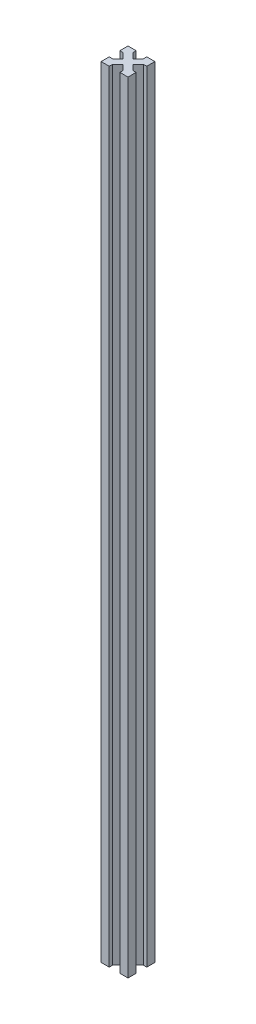
SolidWorks part; units mm, degrees
ref_plane "Plan de face" through (0, 0, 0) normal (0, 0, 1) x (1, 0, 0)
ref_plane "Plan de dessus" through (0, 0, 0) normal (0, 1, 0) x (1, 0, 0)
ref_plane "Plan de droite" through (0, 0, 0) normal (1, 0, 0) x (0, 0, -1)
sketch "Esquisse1" plane through (0, 0, 0) normal (0, 1, 0) x (1, 0, 0)
  line L0 (-2.5, 17.5) -> (-17.5, 17.5)
  line L1 (0, 0) -> (-20, 0)
  line L2 (0, 0) -> (0, 20)
  line L3 (0, 20) -> (-20, 20)
  line L4 (-20, 0) -> (-20, 20)
  line L5 (0, 20) -> (-20, 0) construction
  line L6 (-17.5, 2.5) -> (-17.5, 17.5)
  line L11 (-2.5, 2.5) -> (-17.5, 2.5)
  line L12 (-2.5, 2.5) -> (-2.5, 17.5)
  line L13 (-20, 20) -> (0, 0) construction
  line L14 (-26.9957, 23.4601) -> (-23.4601, 26.9957)
  line L15 (-26.9957, 23.4601) -> (3.4601, -6.9957)
  line L16 (-23.4601, 26.9957) -> (6.9957, -3.4601)
  line L17 (3.4601, -6.9957) -> (6.9957, -3.4601)
  line L18 (-26.9957, 23.4601) -> (6.9957, -3.4601) construction
  line L19 (-23.4601, 26.9957) -> (3.4601, -6.9957) construction
  line L20 (-10, 20) -> (-10, 0) construction
  line L21 (-23.4601, -6.9957) -> (-26.9957, -3.4601)
  line L22 (3.4601, 26.9957) -> (-26.9957, -3.4601)
  line L23 (6.9957, 23.4601) -> (-23.4601, -6.9957)
  line L24 (6.9957, 23.4601) -> (3.4601, 26.9957)
  line L25 (-17.5, 13.9645) -> (-20, 13.9645)
  line L26 (-20, 10) -> (0, 10) construction
  line L27 (-17.5, 6.0355) -> (-20, 6.0355)
  line L28 (-2.5, 6.0355) -> (0, 6.0355)
  line L29 (-2.5, 13.9645) -> (0, 13.9645)
  line L30 (-2.5, 6.0355) -> (0, 6.0355)
  line L31 (-2.5, 13.9645) -> (0, 13.9645)
  line L32 (-13.9645, 2.5) -> (-13.9645, 0)
  line L33 (-6.0355, 17.5) -> (-6.0355, 20)
  line L34 (-13.9645, 17.5) -> (-13.9645, 20)
  line L35 (-6.0355, 2.5) -> (-6.0355, 0)
  point P11 (-10, 10)
  dimension "D1" = 20
  dimension "D2" = 20
  dimension "D3" = 7.3934
  dimension "D4" = 2.5
  dimension "D5" = 43.071
  dimension "D6" = 2.5
extrude "Boss.-Extru.1" add sketch "Esquisse1" along normal blind 580 contours L15 L35 L1 | L16 L12 L11 L15 L1 L2 | L28 L16 L2 | L16 L23 L15 L11 L12 | L32 L23 L1 | L23 L11 L6 L22 L4 L1 | L22 L27 L4 | L23 L15 L22 L6 L11 | L23 L16 L22 L15 | L23 L12 L0 L22 L16 | L23 L2 L3 L22 L0 L12 | L23 L29 L2 | L33 L22 L3 | L16 L34 L3 | L16 L3 L4 L15 L6 L0 | L25 L15 L4 | L22 L16 L0 L6 L15
